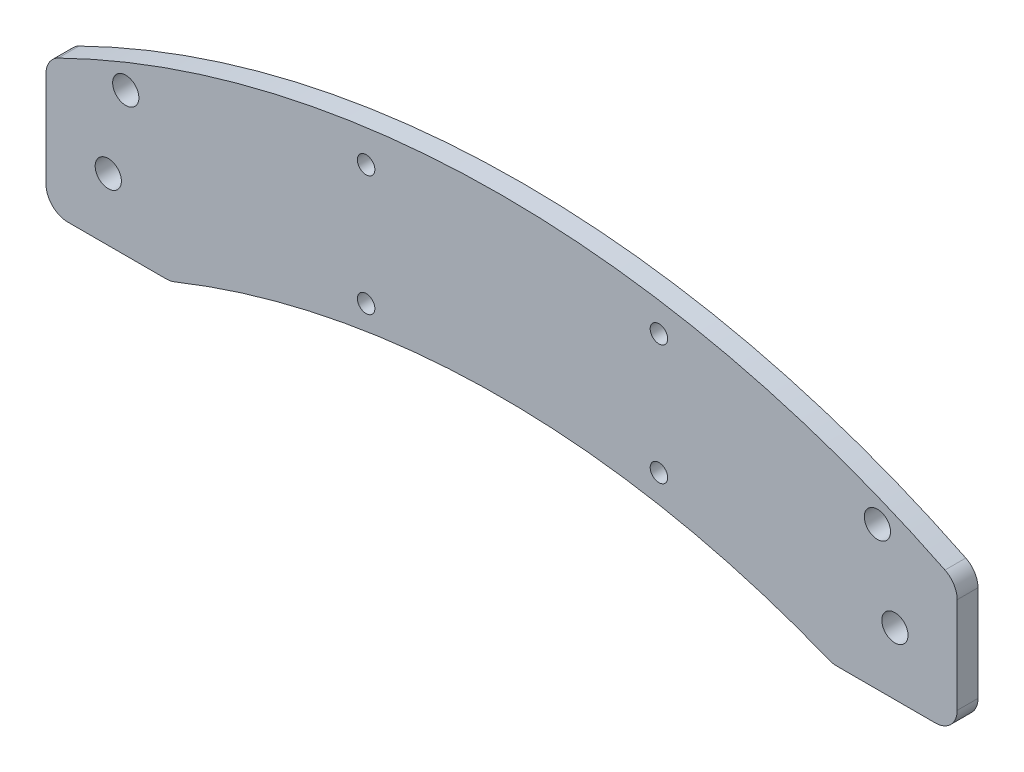
SolidWorks part; units mm, degrees
ref_plane "Front Plane" through (0, 0, 0) normal (0, 0, 1) x (1, 0, 0)
ref_plane "Top Plane" through (0, 0, 0) normal (0, 1, 0) x (1, 0, 0)
ref_plane "Right Plane" through (0, 0, 0) normal (1, 0, 0) x (0, 0, -1)
sketch "Sketch1" plane through (0, 0, 0) normal (0, 0, 1) x (1, 0, 0)
  line L0 (-14.25, -9.25) -> (-14.25, 12.6768)
  line L4 (194.25, 12.6768) -> (194.25, -9.25)
  line L5 (189.25, -14.25) -> (166.7272, -14.25)
  line L9 (13.2728, -14.25) -> (-9.25, -14.25)
  circle A0 centre (59, 31.25) radius 2
  circle A1 centre (59, 3.75) radius 2
  circle A2 centre (126, 31.25) radius 2
  circle A3 centre (126, 3.75) radius 2
  circle A4 centre (180, 0) radius 3
  circle A5 centre (0, 0) radius 3
  arc A6 (164.8558, -13.8866) -> (15.1442, -13.8866) centre (90, -199.3498) ccw
  arc A7 (-11.4556, 17.1641) -> (191.4556, 17.1641) centre (90, -189.25) cw
  circle A8 centre (4, 18.5) radius 3
  circle A9 centre (176, 18.5) radius 3
  arc A10 (194.25, -9.25) -> (189.25, -14.25) centre (189.25, -9.25) cw
  arc A11 (-14.25, -9.25) -> (-9.25, -14.25) centre (-9.25, -9.25) ccw
  arc A12 (166.7272, -14.25) -> (164.8558, -13.8866) centre (166.7272, -9.25) cw
  arc A13 (15.1442, -13.8866) -> (13.2728, -14.25) centre (13.2728, -9.25) cw
  arc A14 (191.4556, 17.1641) -> (194.25, 12.6768) centre (189.25, 12.6768) cw
  arc A15 (-14.25, 12.6768) -> (-11.4556, 17.1641) centre (-9.25, 12.6768) cw
  point P56 (194.25, -14.25)
  point P59 (-14.25, -14.25)
  point P62 (165.75, -14.25)
  point P65 (14.25, -14.25)
  dimension "D1" = 6
  dimension "D2" = 4
  dimension "D3" = 200
  dimension "D4" = 55
  dimension "D5" = 6
  dimension "D6" = 230
  dimension "D7" = 5
  dimension "D8" = 5
  dimension "D9" = 5
  dimension "D10" = 5
  dimension "D11" = 14.25
  dimension "D12" = 14.25
  dimension "D13" = 208.5
  dimension "D14" = 22.5228
extrude "Boss-Extrude1" add sketch "Sketch1" along normal blind 4.7625
sketch "Sketch3" plane through (0, 0, 4.7625) normal (0, 0, 1) x (1, 0, 0)
  line L0 (10.7843, 12.0225) -> (7.7557, -1.9851)
  line L1 (53, 25.6849) -> (53, 14.2358)
  line L2 (132, 24.6472) -> (132, 14.0224)
  line L3 (169.328, 11.5032) -> (172.2443, -1.9851)
  line L4 (12.7252, 20.9989) -> (53, 3.3001) construction
  line L5 (167.2748, 20.9989) -> (132, 2.3232) construction
  line L6 (157.2208, 19.0705) -> (139.3395, 9.6035)
  line L7 (143.43, 4.9801) -> (162.1014, 14.8654)
  line L8 (39.5811, 5.9202) -> (17.683, 15.5433)
  line L9 (24.0389, 19.304) -> (45.9884, 9.6583)
  line L10 (120, 28.3184) -> (120, 10.1639)
  line L11 (65, 28.8348) -> (65, 10.7002)
  arc A0 (162.1014, 14.8654) -> (169.328, 11.5032) centre (164.4409, 10.4465) cw
  arc A1 (132, 24.6472) -> (138.0731, 29.5307) centre (137, 24.6472) cw
  arc A2 (167.1015, -8.3227) -> (12.8985, -8.3227) centre (90, -199.3498) ccw
  arc A3 (165.5242, -7.6936) -> (144.0467, -0.5661) centre (90, -199.3498) ccw
  circle A4 centre (4, 18.5) radius 3 construction
  arc A5 (188.8089, 11.7794) -> (-8.8089, 11.7794) centre (90, -189.25) ccw
  arc A6 (156.7106, 24.5857) -> (138.0731, 29.5307) centre (90, -189.25) ccw
  circle A7 centre (0, 0) radius 3 construction
  circle A8 centre (180, 0) radius 3 construction
  circle A9 centre (176, 18.5) radius 3 construction
  circle A10 centre (126, 31.25) radius 2 construction
  circle A11 centre (59, 31.25) radius 2 construction
  arc A12 (115.5708, 33.2857) -> (69.5434, 33.814) centre (90, -189.25) ccw
  arc A13 (114.4076, 5.1991) -> (70.4739, 5.7227) centre (90, -199.3498) ccw
  arc A14 (132, 14.0224) -> (139.3395, 9.6035) centre (137, 14.0224) ccw
  arc A15 (53, 25.6849) -> (47.0411, 30.5921) centre (48, 25.6849) ccw
  arc A16 (53, 14.2358) -> (45.9884, 9.6583) centre (48, 14.2358) cw
  arc A17 (17.683, 15.5433) -> (10.7843, 12.0225) centre (15.6714, 10.9658) ccw
  arc A18 (157.2208, 19.0705) -> (156.7106, 24.5857) centre (155.8171, 21.7218) ccw
  arc A19 (143.43, 4.9801) -> (144.0467, -0.5661) centre (144.8337, 2.3288) ccw
  arc A20 (39.5811, 5.9202) -> (39.1151, 0.2667) centre (38.3741, 3.1737) cw
  arc A21 (24.0389, 19.304) -> (24.3668, 24.9188) centre (25.2458, 22.0505) cw
  arc A22 (165.5242, -7.6936) -> (172.2443, -1.9851) centre (167.3573, -3.0418) ccw
  arc A23 (14.4758, -7.6936) -> (7.7557, -1.9851) centre (12.6427, -3.0418) cw
  arc A24 (39.1151, 0.2667) -> (14.4758, -7.6936) centre (90, -199.3498) ccw
  arc A25 (47.0411, 30.5921) -> (24.3668, 24.9188) centre (90, -189.25) ccw
  arc A26 (69.5434, 33.814) -> (65, 28.8348) centre (70, 28.8348) ccw
  arc A27 (115.5708, 33.2857) -> (120, 28.3184) centre (115, 28.3184) cw
  arc A28 (114.4076, 5.1991) -> (120, 10.1639) centre (115, 10.1639) ccw
  arc A29 (70.4739, 5.7227) -> (65, 10.7002) centre (70, 10.7002) cw
  point P46 (53, 31.6731)
  dimension "D6" = 8
  dimension "D8" = 6
  dimension "D13" = 5
  dimension "D14" = 3
  dimension "D15" = 5
  dimension "D17" = 6
  dimension "D18" = 5
  dimension "D3" = 8
  dimension "D4" = 8
  dimension "D5" = 8
  dimension "D7" = 6
  dimension "D9" = 3
  dimension "D10" = 6
  dimension "D11" = 3
  dimension "D12" = 6
  dimension "D16" = 6
  dimension "D1" = 6
  dimension "D2" = 6
extrude "Cut-Extrude1" [suppressed] cut sketch "Sketch3" against normal offset from surface (4.35 mm away) 2
sketch "Sketch4" plane through (0, 0, 0) normal (0, 0, 1) x (1, 0, 0)
  line L0 (10, 10) -> (-10, -10) construction
  line L1 (-10, 10) -> (10, 10)
  line L2 (-10, 10) -> (-10, -10)
  line L3 (-10, -10) -> (10, -10)
  line L4 (10, 10) -> (10, -10)
  line L5 (170, 10) -> (190, 10)
  line L6 (170, 10) -> (170, -10)
  line L7 (170, -10) -> (190, -10)
  line L8 (190, 10) -> (190, -10)
  line L9 (190, 10) -> (170, -10) construction
  dimension "D1" = 20
extrude "Cut-Extrude2" cut sketch "Sketch4" along normal blind 0.01
